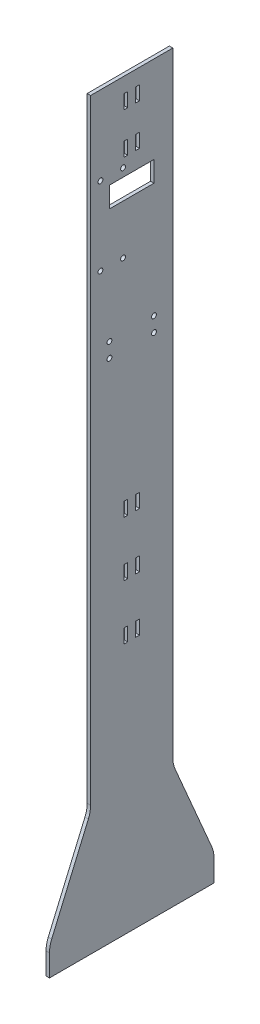
SolidWorks part; units mm, degrees
ref_plane "Front Plane" through (0, 0, 0) normal (0, 0, 1) x (1, 0, 0)
ref_plane "Top Plane" through (0, 0, 0) normal (0, 1, 0) x (1, 0, 0)
ref_plane "Right Plane" through (0, 0, 0) normal (1, 0, 0) x (0, 0, -1)
sketch "Sketch1" plane through (0, 0, 0) normal (1, 0, 0) x (0, 0, -1)
  line L1 (-38.1, 457.2) -> (38.1, 457.2)
  line L2 (-38.1, 457.2) -> (-38.1, -457.2)
  line L3 (-38.1, -457.2) -> (38.1, -457.2)
  line L4 (38.1, 457.2) -> (38.1, -457.2)
  line L5 (-38.1, 457.2) -> (38.1, -457.2) construction
  line L6 (-38.1, -457.2) -> (38.1, 457.2) construction
  point P0 (0, 0)
  dimension "D1" = 914.4
  dimension "D2" = 76.2
extrude "Boss-Extrude1" add sketch "Sketch1" along normal blind 3.175
sketch "Sketch2" plane through (3.175, 0, 0) normal (1, 0, 0) x (0, 0, -1)
  line L0 (-38.1, -457.2) -> (38.1, -457.2) construction
  line L1 (3.722, -204.5335) -> (7.278, -204.5335)
  line L2 (3.722, -204.5335) -> (3.722, -217.4875)
  line L3 (3.722, -217.4875) -> (7.278, -217.4875)
  line L4 (7.278, -204.5335) -> (7.278, -217.4875)
  line L5 (3.722, -204.5335) -> (7.278, -217.4875) construction
  line L6 (3.722, -217.4875) -> (7.278, -204.5335) construction
  point P0 (5.5, -211.0105)
  dimension "D1" = 3.556
  dimension "D2" = 12.954
  dimension "D3" = 239.7125
  dimension "D4" = 3.722
extrude "Cut-Extrude1" cut sketch "Sketch2" against normal through all
mirror "Mirror1" about plane through (0, 0, 0) normal (0, 0, 1) of "Cut-Extrude1"
pattern_linear "LPattern1" count 2 spacing 50.8 along (0, 1, 0) count 2 spacing 50.8 along (0, -1, 0) of "Mirror1", "Cut-Extrude1"
sketch "Sketch3" plane through (3.175, 0, 0) normal (1, 0, 0) x (0, 0, -1)
  line L0 (7.278, -166.6875) -> (7.278, -153.7335) construction
  line L1 (3.722, 135.1915) -> (7.278, 135.1915)
  line L2 (3.722, 135.1915) -> (3.722, 122.2375)
  line L3 (3.722, 122.2375) -> (7.278, 122.2375)
  line L4 (7.278, 135.1915) -> (7.278, 122.2375)
  line L5 (3.722, 135.1915) -> (7.278, 122.2375) construction
  line L6 (3.722, 122.2375) -> (7.278, 135.1915) construction
  line L7 (7.278, -153.7335) -> (3.722, -153.7335) construction
  line L8 (3.722, -153.7335) -> (3.722, -166.6875) construction
  line L9 (0, 0) -> (0, 52.1648) construction
  line L10 (-3.722, 122.2375) -> (-7.278, 135.1915) construction
  line L11 (-3.722, 135.1915) -> (-7.278, 122.2375) construction
  line L12 (-7.278, 135.1915) -> (-7.278, 122.2375)
  line L13 (-3.722, 122.2375) -> (-7.278, 122.2375)
  line L14 (-3.722, 135.1915) -> (-3.722, 122.2375)
  line L15 (-3.722, 135.1915) -> (-7.278, 135.1915)
  point P0 (5.5, 128.7145)
  point P18 (-5.5, 128.7145)
  dimension "D1" = 275.971
extrude "Cut-Extrude2" cut sketch "Sketch3" against normal through all
pattern_linear "LPattern2" count 2 spacing 38.1 along (0, 1, 0) of "Cut-Extrude2"
sketch "Sketch4" plane through (3.175, 0, 0) normal (1, 0, 0) x (0, 0, -1)
  line L0 (0, -457.2) -> (0, 187.325) construction
  line L1 (-38.1, -457.2) -> (38.1, -457.2) construction
  line L2 (0, 187.325) -> (-38.1, 187.325)
  line L3 (-38.1, 457.2) -> (-38.1, -457.2) construction
  line L4 (-38.1, 187.325) -> (38.1, 187.325)
  line L5 (38.1, -457.2) -> (38.1, 457.2) construction
  line M30 (38.1, -457.2) -> (38.1, 457.2)
  line M31 (38.1, 457.2) -> (-38.1, 457.2)
  line M32 (-38.1, 457.2) -> (-38.1, -457.2)
  dimension "D1" = 644.525
extrude "Cut-Extrude3" cut sketch "Sketch4" against normal through all contours L2 L4 M30 M31 M32
sketch "Sketch5" plane through (3.175, 0, 0) normal (1, 0, 0) x (0, 0, -1)
  line L0 (-38.1, -457.2) -> (-38.1, -501.65)
  line L1 (-38.1, -501.65) -> (38.1, -501.65)
  line L2 (38.1, -501.65) -> (38.1, -457.2)
  line L7 (38.1, -457.2) -> (38.1, 187.325)
  line L8 (38.1, 187.325) -> (-38.1, 187.325)
  line L9 (-38.1, 187.325) -> (-38.1, -457.2)
  line L10 (-38.1, -457.2) -> (38.1, -457.2)
  line L14 (-38.1, -457.2) -> (38.1, -457.2)
  dimension "D1" = 44.45
  dimension "D2" = 0
extrude "Boss-Extrude2" add sketch "Sketch5" against normal up to surface (3.175 mm away) up to face at (0, -160.2105, 5.5)
sketch "Sketch6" plane through (3.175, 0, 0) normal (1, 0, 0) x (0, 0, -1)
  line L1 (-20.6375, 106.6318) -> (20.6375, 106.6318)
  line L2 (-20.6375, 106.6318) -> (-20.6375, 87.5818)
  line L4 (20.6375, 106.6318) -> (20.6375, 87.5818)
  line L5 (0, 187.325) -> (0, 38.8722) construction
  line L6 (38.1, 187.325) -> (-38.1, 187.325) construction
  line L7 (-20.6375, 87.5818) -> (20.6375, 87.5818)
  line L8 (-39.114, 119.3318) -> (2.161, 119.3318) construction
  point P6 (0, 106.6318)
  dimension "D1" = 19.05
  dimension "D2" = 41.275
  dimension "D3" = 12.7
extrude "Cut-Extrude4" cut sketch "Sketch6" against normal through all contours L7 L4 L1 L2
sketch "Sketch7" plane through (3.175, 0, 0) normal (1, 0, 0) x (0, 0, -1)
  line L0 (-76.2, -501.65) -> (76.2, -501.65)
  line L1 (76.2, -501.65) -> (76.2, -476.25)
  line L2 (76.2, -476.25) -> (38.1, -387.35)
  line L3 (38.1, -501.65) -> (38.1, 187.325) construction
  line L4 (38.1, -387.35) -> (-38.1, -387.35)
  line L5 (-38.1, 187.325) -> (-38.1, -501.65) construction
  line L6 (-38.1, -387.35) -> (-76.2, -476.25)
  line L7 (-76.2, -476.25) -> (-76.2, -501.65)
  line L8 (-38.1, -501.65) -> (38.1, -501.65) construction
  dimension "D1" = 152.4
  dimension "D2" = 38.1
  dimension "D3" = 25.4
  dimension "D4" = 114.3
extrude "Boss-Extrude3" add sketch "Sketch7" against normal blind 3.175
fillet "Fillet1" radius 25.4 4 edges at (1.5875, -476.25, 76.2) (1.5875, -387.35, 38.1) (1.5875, -476.25, -76.2) (1.5875, -387.35, -38.1)
hole_wizard "#8 Clearance Hole1" positions "Sketch8" profile "Sketch9" hole size "#8" standard "ANSI Inch" end condition through all
sketch "Sketch8" plane through (3.175, 0, 0) normal (1, 0, 0) x (0, 0, -1)
  point P0 (-7.999, 41.8618)
  point P3 (-28.954, 41.8618)
  point P6 (20.6375, -18.8258)
  point P9 (-20.6375, -18.8258)
  point P12 (20.6375, -32.3008)
  point P15 (-20.6375, -32.3008)
  point P19 (-7.999, 114.2518)
  point P22 (-28.954, 114.2518)
sketch "Sketch9" plane through (3.175, 41.8618, 7.999) normal (0, 1, 0) x (0, 0, -1)
  line L0 (0, 0) -> (0, 3.175)
  line L1 (0, 3.175) -> (2.2479, 3.175)
  line L2 (2.2479, 3.175) -> (2.2479, 0)
  line L5 (2.2479, 0) -> (0, 0)
  line L11 (0, -6.35) -> (0, 107.95) construction
  dimension "Thru Hole Dia." = 4.4958
  dimension "Thru Hole Depth" = 3.175
